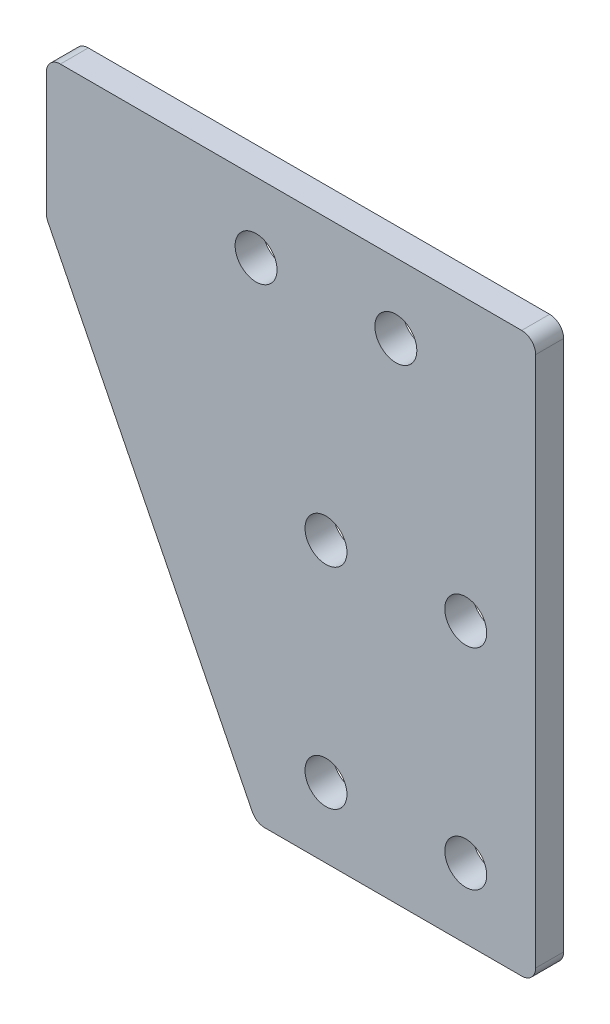
SolidWorks part; units mm, degrees
material "环氧板3240"
ref_plane "前视基准面" through (0, 0, 0) normal (0, 0, 1) x (1, 0, 0)
ref_plane "上视基准面" through (0, 0, 0) normal (0, 1, 0) x (1, 0, 0)
ref_plane "右视基准面" through (0, 0, 0) normal (1, 0, 0) x (0, 0, -1)
other "Configuration Table"
sketch "草图1" plane through (0, 0, 0) normal (0, 0, 1) x (1, 0, 0)
  line L0 (-30, -5) -> (-30, 5)
  line L1 (-30, 5) -> (5, 5)
  line L2 (5, 5) -> (5, -35)
  line L3 (5, -35) -> (-15, -35)
  line L4 (-15, -35) -> (-30, -5)
  line L5 (-30, 0) -> (5, 0) construction
  line L6 (0, -35) -> (0, 5) construction
  line L7 (-10, -35) -> (-10, 5) construction
  line L8 (-10, -15) -> (0, -15) construction
  line L9 (-10, -30) -> (0, -30) construction
  circle A0 centre (-15, 0) radius 1.5
  circle A1 centre (-5, 0) radius 1.5
  circle A2 centre (-10, -15) radius 1.5
  circle A3 centre (-10, -30) radius 1.5
  circle A4 centre (0, -30) radius 1.5
  circle A5 centre (0, -15) radius 1.5
  dimension "D7" = 3
  dimension "D8" = 10
  dimension "D9" = 15
  dimension "D10" = 15
  dimension "D11" = 5
  dimension "D12" = 15.8114
  dimension "D13" = 5
  dimension "D1" = 20
  dimension "D2" = 10
  dimension "D3" = 35
  dimension "D4" = 40
  dimension "D5" = 10
  dimension "D6" = 5
extrude "凸台-拉伸1" add sketch "草图1" along normal blind 2
fillet "圆角1" radius 1 5 edges at (5, -35, 1) (-15, -35, 1) (5, 5, 1) (-30, -5, 1) (-30, 5, 1)
